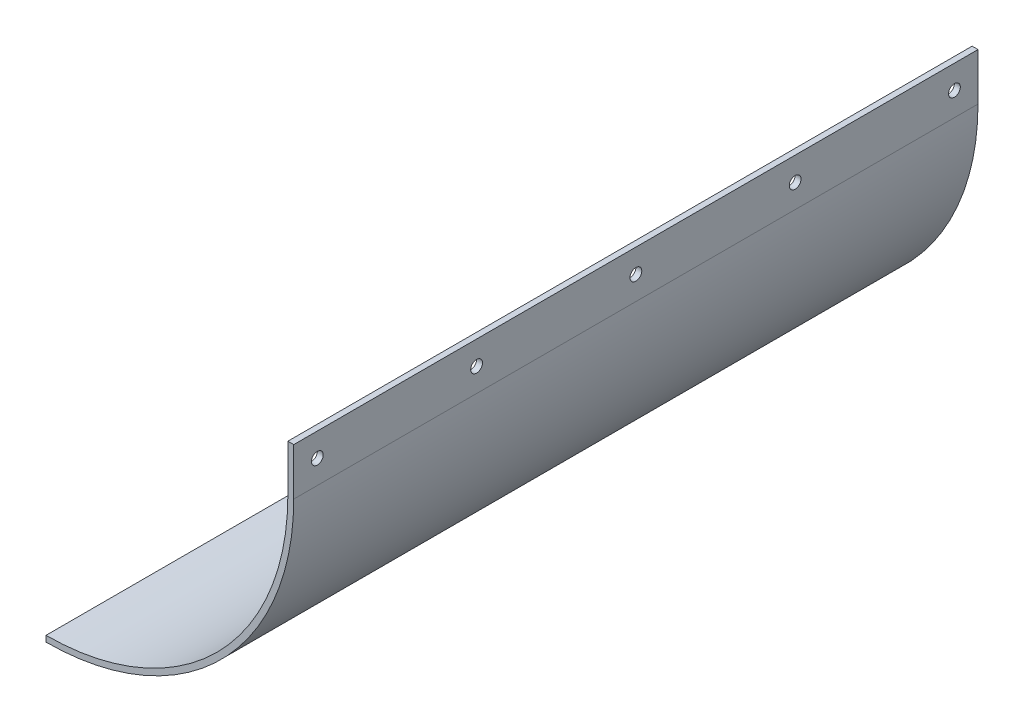
SolidWorks part; units mm, degrees
ref_plane "Front Plane" through (0, 0, 0) normal (0, 0, 1) x (1, 0, 0)
ref_plane "Top Plane" through (0, 0, 0) normal (0, 1, 0) x (1, 0, 0)
ref_plane "Right Plane" through (0, 0, 0) normal (1, 0, 0) x (0, 0, -1)
sketch "Sketch1" plane through (0, 0, 0) normal (0, 0, 1) x (1, 0, 0)
  line L0 (0, -133.35) -> (0, -130.175)
  line L1 (130.175, 0) -> (130.175, 25.4)
  line L2 (130.175, 25.4) -> (133.35, 25.4)
  line L3 (133.35, 25.4) -> (133.35, 0)
  arc A0 (130.175, 0) -> (0, -130.175) centre (0, 0) cw
  arc A1 (133.35, 0) -> (0, -133.35) centre (0, 0) cw
  dimension "D1" = 3.175
  dimension "D2" = 25.4
  dimension "D3" = 130.175
extrude "Boss-Extrude1" add sketch "Sketch1" along normal mid plane 368.3 contours A1 L0 A0 L1 L2 L3
sketch "Sketch2" plane through (133.35, 0, 0) normal (1, 0, 0) x (0, 0, -1)
  line L0 (-171.45, 12.7) -> (-85.725, 12.7) construction
  line L1 (-85.725, 12.7) -> (0, 12.7) construction
  line L2 (0, 12.7) -> (85.725, 12.7) construction
  line L3 (85.725, 12.7) -> (171.45, 12.7) construction
  line L4 (171.45, 12.7) -> (184.15, 12.7) construction
  line L5 (184.15, 25.4) -> (184.15, 0) construction
  line L6 (-171.45, 12.7) -> (-184.15, 12.7) construction
  line L7 (-184.15, 25.4) -> (-184.15, 0) construction
  line L8 (0, 0) -> (0, 12.7) construction
  line L9 (-184.15, 0) -> (184.15, 0) construction
  line L10 (0, 12.7) -> (0, 25.4) construction
  line L11 (-184.15, 25.4) -> (184.15, 25.4) construction
  circle A0 centre (0, 12.7) radius 3.175
  circle A1 centre (85.725, 12.7) radius 3.175
  circle A2 centre (-85.725, 12.7) radius 3.175
  circle A3 centre (-171.45, 12.7) radius 3.175
  circle A4 centre (171.45, 12.7) radius 3.175
  dimension "D1" = 6.35
  dimension "D2" = 12.7
extrude "Cut-Extrude1" cut sketch "Sketch2" against normal blind 381
